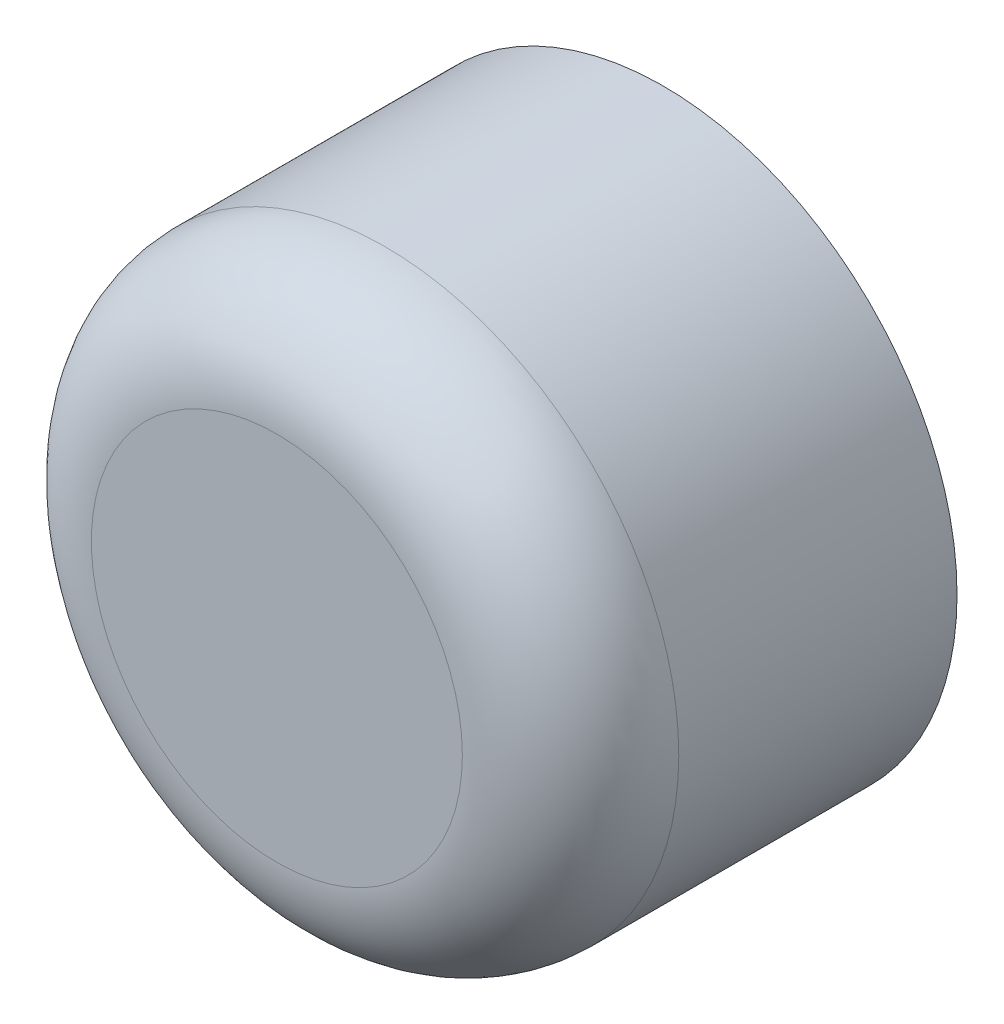
SolidWorks part; units mm, degrees
ref_plane "前基準面" through (0, 0, 0) normal (0, 0, 1) x (1, 0, 0)
ref_plane "上基準面" through (0, 0, 0) normal (0, 1, 0) x (1, 0, 0)
ref_plane "右基準面" through (0, 0, 0) normal (1, 0, 0) x (0, 0, -1)
sketch "草圖1" plane through (0, 0, 0) normal (0, 0, 1) x (1, 0, 0)
  circle A0 centre (0, 0) radius 19
  dimension "D1" = 38
extrude "填料-伸長1" add sketch "草圖1" along normal blind 25 contours A0
sketch "草圖2" plane through (0, 0, 0) normal (0, 0, -1) x (-1, 0, 0)
  circle A0 centre (0, 0) radius 10
  dimension "D1" = 20
extrude "除料-伸長1" cut sketch "草圖2" against normal blind 5 contours A0
sketch "草圖3" plane through (0, 0, 5) normal (0, 0, -1) x (-1, 0, 0)
  circle A0 centre (0, 0) radius 3
  dimension "D1" = 6
extrude "除料-伸長2" cut sketch "草圖3" against normal blind 15 contours A0
sketch "草圖4" plane through (0, 0, 0) normal (0, 1, 0) x (1, 0, 0)
  line L0 (19, -25) -> (19, 0) construction
  line L1 (19, 0) -> (-19, 0) construction
  circle A0 centre (0, -10) radius 1.1
  dimension "D2" = 2.2
  dimension "D1" = 19
  dimension "D3" = 10
extrude "除料-伸長3" cut sketch "草圖4" against normal up to next
fillet "圓角1" radius 7 1 edges at (19, 0, 25)
